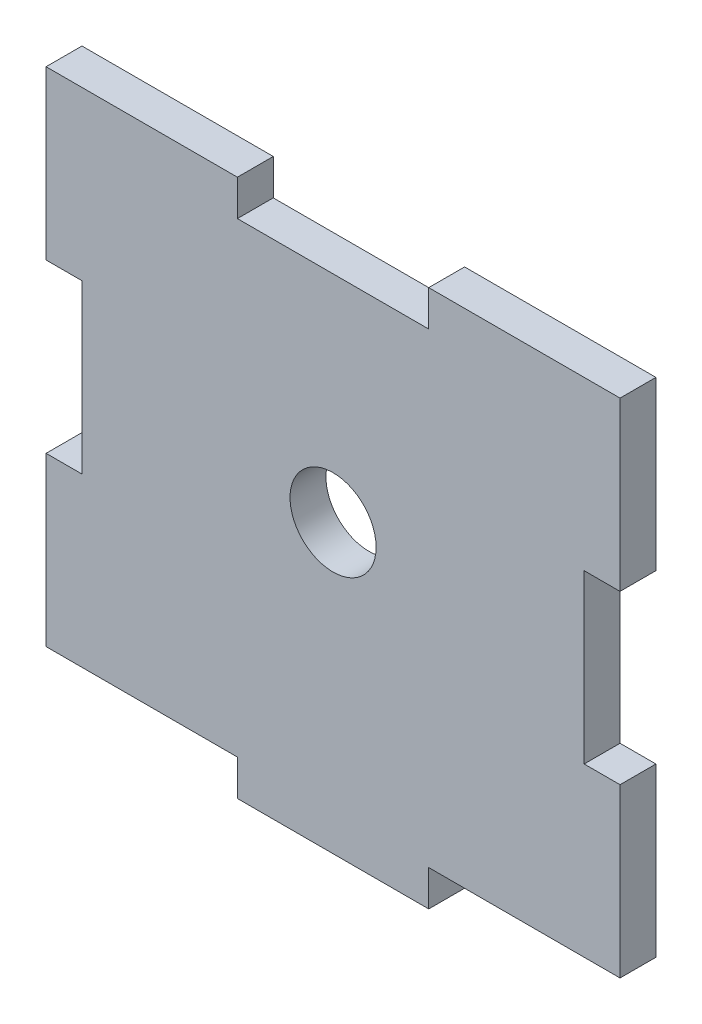
SolidWorks part; units mm, degrees
ref_plane "Alzado" through (0, 0, 0) normal (0, 0, 1) x (1, 0, 0)
ref_plane "Planta" through (0, 0, 0) normal (0, 1, 0) x (1, 0, 0)
ref_plane "Vista lateral" through (0, 0, 0) normal (1, 0, 0) x (0, 0, -1)
sketch "Croquis1" plane through (0, 0, 0) normal (0, 0, 1) x (1, 0, 0)
  line L0 (40, 75) -> (40, 48.9607) construction
  line L1 (0, 0) -> (80, 0)
  line L2 (0, 0) -> (0, 75)
  line L3 (0, 75) -> (80, 75)
  line L4 (80, 0) -> (80, 75)
  line L5 (0, 75) -> (5, 75)
  line L6 (0, 75) -> (0, 0)
  line L7 (0, 0) -> (5, 0)
  line L8 (5, 75) -> (5, 0)
  line L9 (0, 0) -> (80, 0)
  line L10 (0, 0) -> (0, 5)
  line L11 (0, 5) -> (80, 5)
  line L12 (80, 0) -> (80, 5)
  line L13 (26.6667, 5) -> (26.6667, 0)
  line L14 (53.3333, 5) -> (53.3333, 0)
  line L15 (0, 51.6667) -> (5, 51.6667)
  line L16 (0, 28.3333) -> (5, 28.3333)
  line L17 (75, 75) -> (75, 0)
  line L18 (80, 28.3333) -> (75, 28.3333)
  line L19 (80, 51.6667) -> (75, 51.6667)
  point P19 (53.3333, 2.5)
  dimension "D1" = 80
  dimension "D2" = 75
  dimension "D3" = 5
  dimension "D4" = 5
  dimension "D5" = 23.3333
  dimension "D6" = 23.3333
  dimension "D7" = 26.6667
  dimension "D8" = 26.6667
extrude "Saliente-Extruir1" add sketch "Croquis1" along normal blind 5
sketch "Croquis2" plane through (0, 0, 5) normal (0, 0, 1) x (1, 0, 0)
  line L0 (0, 75) -> (80, 75) construction
  line L1 (53.3333, 75) -> (26.6667, 75)
  line L2 (53.3333, 75) -> (53.3333, 70)
  line L3 (53.3333, 70) -> (26.6667, 70)
  line L4 (26.6667, 75) -> (26.6667, 70)
  line L6 (0, 51.6667) -> (0, 75) construction
  line L7 (80, 51.6667) -> (80, 75) construction
  dimension "D1" = 5
  dimension "D2" = 26.6667
  dimension "D3" = 26.6667
extrude "Cortar-Extruir1" cut sketch "Croquis2" against normal blind 10
sketch "Croquis5" plane through (0, 0, 5) normal (0, 0, 1) x (1, 0, 0)
  line L0 (40, 70) -> (40, 40)
  line L1 (26.6667, 70) -> (53.3333, 70) construction
  line L2 (75, 40) -> (40, 40)
  line L3 (75, 51.6667) -> (75, 28.3333) construction
  circle A0 centre (40, 40) radius 6
  point P0 (0, 0)
  point P10 (0, 0)
  dimension "D1" = 12
extrude "Cortar-Extruir3" cut sketch "Croquis5" against normal blind 10 contours L0 A0 L2 | L2 A0 L0
sketch "Croquis6" plane through (0, 0, 5) normal (0, 0, 1) x (1, 0, 0)
  line L20 (53.3333, 75) -> (53.3333, 70)
  line L21 (53.3333, 70) -> (26.6667, 70)
  line L22 (26.6667, 70) -> (26.6667, 75)
  line L23 (26.6667, 75) -> (0, 75)
  line L24 (0, 75) -> (0, 51.6667)
  line L25 (0, 51.6667) -> (5, 51.6667)
  line L26 (5, 51.6667) -> (5, 28.3333)
  line L27 (5, 28.3333) -> (0, 28.3333)
  line L28 (0, 28.3333) -> (0, 5)
  line L29 (0, 5) -> (26.6667, 5)
  line L30 (26.6667, 5) -> (26.6667, 0)
  line L31 (26.6667, 0) -> (53.3333, 0)
  line L32 (53.3333, 0) -> (53.3333, 5)
  line L33 (53.3333, 5) -> (80, 5)
  line L34 (80, 5) -> (80, 28.3333)
  line L35 (80, 28.3333) -> (75, 28.3333)
  line L36 (75, 28.3333) -> (75, 51.6667)
  line L37 (75, 51.6667) -> (80, 51.6667)
  line L38 (80, 51.6667) -> (80, 75)
  line L39 (80, 75) -> (53.3333, 75)
  line L40 (53.3333, 75) -> (53.3333, 70)
  line L41 (53.3333, 70) -> (26.6667, 70)
  line L42 (26.6667, 70) -> (26.6667, 75)
  line L43 (26.6667, 75) -> (0, 75)
  line L44 (0, 75) -> (0, 51.6667)
  line L45 (0, 51.6667) -> (5, 51.6667)
  line L46 (5, 51.6667) -> (5, 28.3333)
  line L47 (5, 28.3333) -> (0, 28.3333)
  line L48 (0, 28.3333) -> (0, 5)
  line L49 (0, 5) -> (26.6667, 5)
  line L50 (26.6667, 5) -> (26.6667, 0)
  line L51 (26.6667, 0) -> (53.3333, 0)
  line L52 (53.3333, 0) -> (53.3333, 5)
  line L53 (53.3333, 5) -> (80, 5)
  line L54 (80, 5) -> (80, 28.3333)
  line L55 (80, 28.3333) -> (75, 28.3333)
  line L56 (75, 28.3333) -> (75, 51.6667)
  line L57 (75, 51.6667) -> (80, 51.6667)
  line L58 (80, 51.6667) -> (80, 75)
  line L59 (80, 75) -> (53.3333, 75)
  circle A0 centre (40, 40) radius 6 construction
  circle A1 centre (40, 40) radius 6
  dimension "D1" = 0
